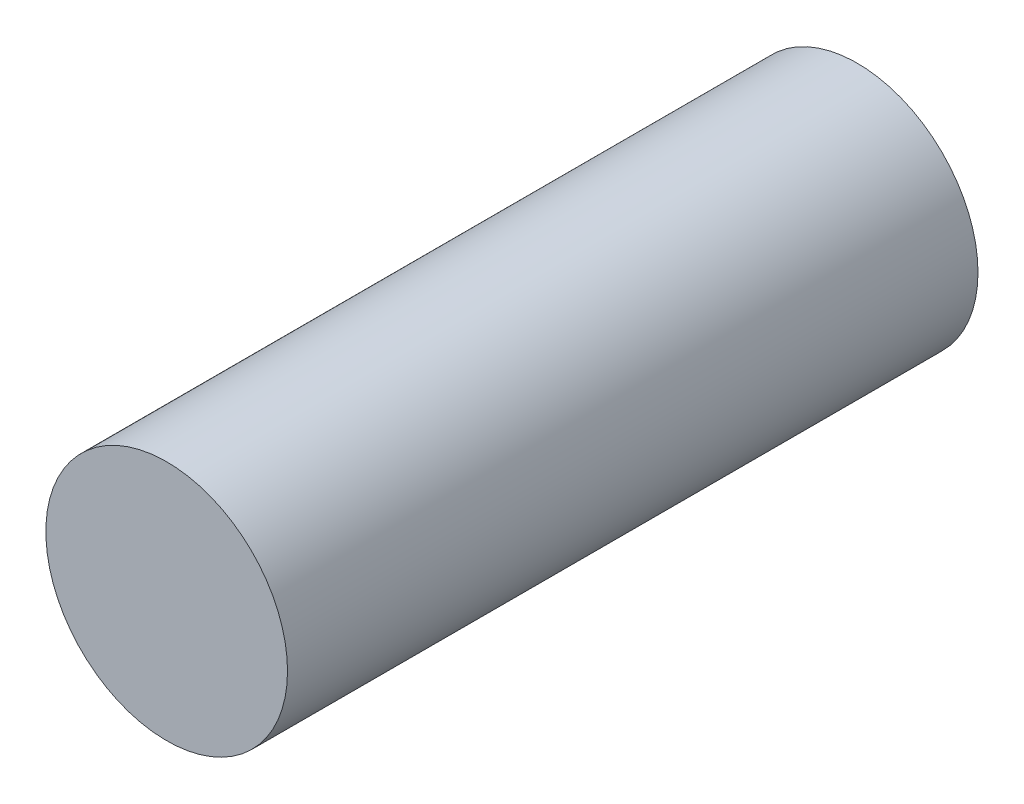
SolidWorks part; units mm, degrees
ref_plane "Alzado" through (0, 0, 0) normal (0, 0, 1) x (1, 0, 0)
ref_plane "Planta" through (0, 0, 0) normal (0, 1, 0) x (1, 0, 0)
ref_plane "Vista lateral" through (0, 0, 0) normal (1, 0, 0) x (0, 0, -1)
sketch "Croquis1" plane through (0, 0, 0) normal (0, 0, 1) x (1, 0, 0)
  circle A0 centre (0, 0) radius 17.5
  dimension "D1" = 35
extrude "Saliente-Extruir1" add sketch "Croquis1" along normal blind 100
